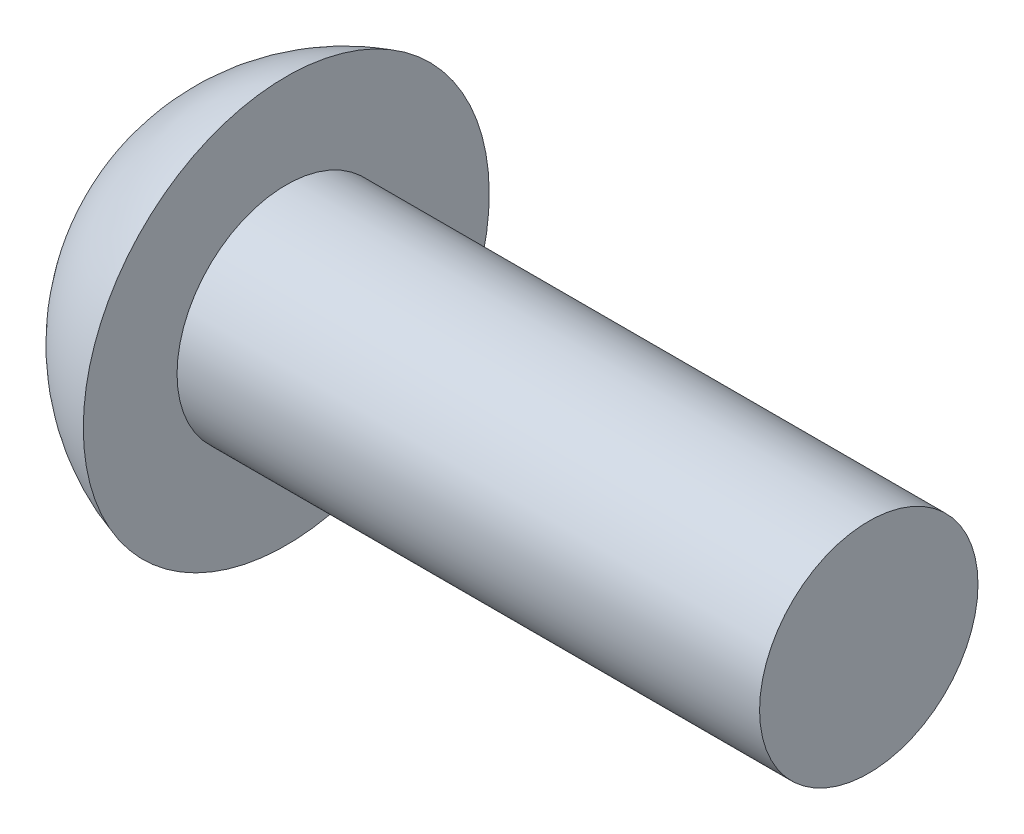
SolidWorks part; units mm, degrees
ref_plane "Plane1" through (0, 0, 0) normal (0, 0, 1) x (1, 0, 0)
ref_plane "Plane2" through (0, 0, 0) normal (0, 1, 0) x (1, 0, 0)
ref_plane "Plane3" through (0, 0, 0) normal (1, 0, 0) x (0, 0, -1)
sketch "BodySke" plane through (0, 0, 0) normal (0, 0, 1) x (1, 0, 0)
  line L0 (2.1, 1.5) -> (2.1, 2.7875)
  line L1 (2.6, 15.875) -> (2.6, -8.7304) construction
  line L2 (-25.4, 0) -> (127, 0) construction
  line L3 (10.1, 0) -> (0, 0)
  line L4 (2.1, 1.5) -> (10.1, 1.5)
  line L5 (10.1, 1.5) -> (10.1, 0)
  line L8 (2.1, 0.7946) -> (2.1, -8.7304) construction
  arc A0 (2.1, 2.7875) -> (0, 0) centre (2.9, 0) ccw
  dimension "Advance" = 0.5
revolve "Base-Revolve" add sketch "BodySke" angle 360 about L2
cosmetic thread "ThreadCosmetic" parameters "Thread_length"=7, "Thread_minor"=2.459
sketch "Sketch3" plane through (0, 0, 0) normal (1, 0, 0) x (0, 0, -1)
  line L0 (0.265, -1.5) -> (-0.265, -1.5)
  line L1 (0.265, -1.5) -> (0.265, 1.5)
  line L2 (-0.265, 1.5) -> (0.265, 1.5)
  line L3 (-0.265, 1.5) -> (-0.265, -1.5)
ref_plane "Plane4" through (1.7, 0, 0) normal (1, 0, 0) x (0, 0, -1)
sketch "Sketch4" plane through (1.7, 0, 0) normal (1, 0, 0) x (0, 0, -1)
  line L0 (0.265, -0.6524) -> (-0.265, -0.6524)
  line L1 (0.265, -0.6524) -> (0.265, 0.6524)
  line L2 (-0.265, 0.6524) -> (0.265, 0.6524)
  line L3 (-0.265, 0.6524) -> (-0.265, -0.6524)
loft "Recess" cut profiles "Sketch3", "Sketch4"
pattern_circular "RecPat" count 2 every 90 about axis through (0, 0, 0) along (1, 0, 0) of "Recess"
sketch "RecCorSke" plane through (0, 0, 0) normal (0, 0, 1) x (1, 0, 0)
  line L0 (-3.175, 0) -> (15.875, 0) construction
  line L1 (-25.4, 0) -> (127, 0) construction
  line L2 (0, 0) -> (0, 0.6749)
  line L3 (0, 0.6749) -> (1.7, 0.556)
  line L4 (1.7, 0.556) -> (1.8807, 0)
  line L5 (1.8807, 0) -> (0, 0)
  dimension "Draft_angle" = 4
  dimension "Bottom_angle" = 18
revolve "RecessCore" cut sketch "RecCorSke" angle 360 about L0
sketch "Sketch5" plane through (0, 0, 0) normal (1, 0, 0) x (0, 0, -1)
  line L0 (-0.45, -2.7509) -> (-0.45, 2.7509)
  line L1 (0, 2.7875) -> (0, -2.7875) construction
  line L2 (0.45, -2.7509) -> (0.45, 2.7509)
  circle A0 centre (0, 0) radius 2.7875 construction
  arc A1 (0.45, 2.7509) -> (-0.45, 2.7509) centre (0, 0) ccw
  arc A2 (-0.45, -2.7509) -> (0.45, -2.7509) centre (0, 0) ccw
  dimension "Slot_width" = 0.9
extrude "Slot" [suppressed] cut sketch "Sketch5" along normal blind 1.2
equation "\"D1@Sketch3\" = \"Cross_dia@Sketch3\" / 2"
equation "\"D2@Sketch3\" = \"Cross_width@Sketch3\" / 2"
equation "\"Depth@RecCorSke\" = \"Cross_depth@Plane4\""
equation "\"D1@Sketch4\" = \"Cross_width@Sketch3\""
equation "\"D2@Sketch4\" = \"Cross_dia@Sketch3\" - 2.0 * \"Cross_depth@Plane4\" * tan(26.5  * 0.017453292)"
equation "\"D3@Sketch4\" = \"D1@Sketch4\" / 2"
equation "\"D4@Sketch4\" = \"D2@Sketch4\" / 2"
equation "\"Thread_length@ThreadCosmetic\" = ((sgn( (\"Length@BodySke\" - \"Advance@BodySke\" * 2.0 ) - \"Thread_nom@BodySke\" )-1)*( (\"Length@BodySke\" - \"Advance@BodySke\" * 2.0 ) - \"Thread_nom@BodySke\" ))/-2+ \"Thread_nom@BodySke\""
